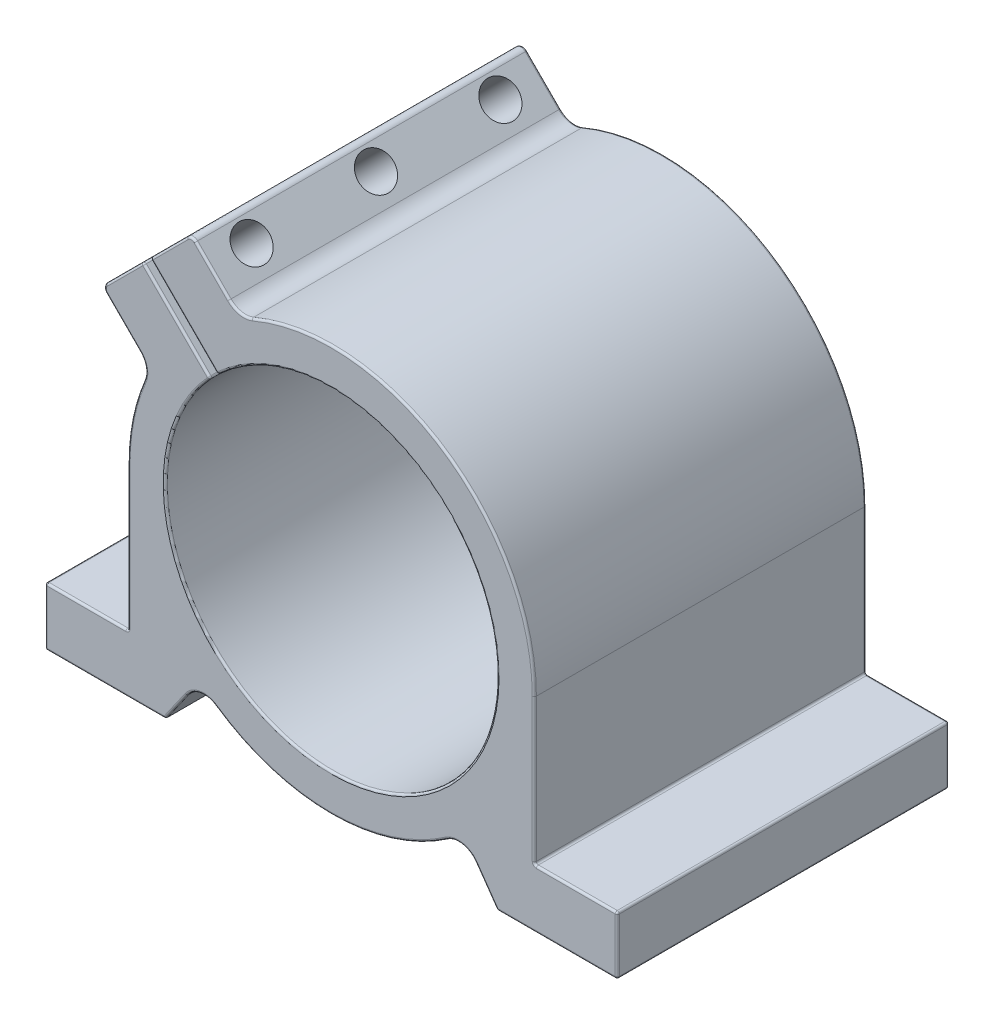
SolidWorks part; units mm, degrees
ref_plane "Спереди" through (0, 0, 0) normal (0, 0, 1) x (1, 0, 0)
ref_plane "Сверху" through (0, 0, 0) normal (0, 1, 0) x (1, 0, 0)
ref_plane "Справа" through (0, 0, 0) normal (1, 0, 0) x (0, 0, -1)
sketch "Эскиз1" plane through (0, 0, 0) normal (0, 0, 1) x (1, 0, 0)
  line L0 (165.1506, 443.0816) -> (1085.1506, 443.0816) construction
  line L1 (0, 0) -> (0, -49) construction
  line L2 (69, -49) -> (-69, -49)
  line L3 (-69, -49) -> (-69, -35)
  line L4 (-69, -35) -> (-49, -35)
  line L5 (-49, -35) -> (-49, 0)
  line L6 (-45.4178, 43.65) -> (-0.8839, -0.8839)
  line L7 (-45.4178, 43.65) -> (-55.3173, 33.7505)
  line L8 (-0.8839, -0.8839) -> (-10.7834, -10.7834)
  line L9 (-55.3173, 33.7505) -> (-10.7834, -10.7834)
  line L10 (-43.65, 45.4178) -> (0.8839, 0.8839)
  line L11 (-43.65, 45.4178) -> (-33.7505, 55.3173)
  line L12 (0.8839, 0.8839) -> (10.7834, 10.7834)
  line L13 (-33.7505, 55.3173) -> (10.7834, 10.7834)
  line L14 (-40, -49) -> (-31.7957, -37.2831)
  line L15 (49, -35) -> (49, 0)
  line L16 (69, -35) -> (49, -35)
  line L17 (69, -49) -> (69, -35)
  line L18 (40, -49) -> (31.7957, -37.2831)
  circle A0 centre (0, 0) radius 40
  circle A1 centre (0, 0) radius 49
  point P11 (-27.3866, 29.1543)
  dimension "D1" = 80
  dimension "D2" = 49
  dimension "D3" = 23
  dimension "D4" = 2.5
  dimension "D5" = 1.25
  dimension "D6" = 1.25
  dimension "D7" = 14
  dimension "D8" = 14
  dimension "D9" = 20
  dimension "D10" = 138
  dimension "D11" = 45
  dimension "D12" = 14
  dimension "D13" = 55
  dimension "D14" = 29
extrude "Бобышка-Вытянуть1" add sketch "Эскиз1" along normal mid plane 80 contours A1 L5 L4 L3 L2 L14 | A1 L13 A0 L9 | A1 L18 L2 L17 L16 L15 | A1 L6 L7 L9 | A1 L13 L11 L10 | L6 A1 L9 A0 | L13 A1 L10 A0
fillet "Скругление1" radius 5 4 edges at (31.7957, -37.2831, 0) (-31.7957, -37.2831, 0) (-43.7109, 22.1441, 0) (-22.1441, 43.7109, 0)
sketch "Эскиз2" plane through (10.7834, 10.7834, 0) normal (0.7071, 0.7071, 0) x (0, 0, -1)
  line L0 (-40, 56.5199) -> (40, 56.5199) construction
  line L1 (-40, 62.9805) -> (-40, 50.0593) construction
  line L2 (40, 62.9805) -> (40, 50.0593) construction
  circle A0 centre (-30, 56.5199) radius 4.25
  circle A1 centre (0, 56.5199) radius 4.25
  circle A2 centre (30, 56.5199) radius 4.25
  dimension "D1" = 8.5
  dimension "D2" = 30
  dimension "D3" = 30
extrude "Вырез-Вытянуть1" cut sketch "Эскиз2" against normal up to surface (16.5 mm away) up to face at (-37.2861, 35.5183, 0)
sketch "Эскиз3" plane through (-0.8839, -0.8839, 0) normal (0.7071, 0.7071, 0) x (0, 0, -1)
  circle A0 centre (-30, 56.5199) radius 3.1
  circle A1 centre (0, 56.5199) radius 3.1
  circle A2 centre (30, 56.5199) radius 3.1
  dimension "D1" = 6.2
extrude "Вырез-Вытянуть2" cut sketch "Эскиз3" against normal blind 80
fillet "Скругление2" radius 1.5 2 edges at (-55.3173, 33.7505, 0) (-33.7505, 55.3173, 0)
fillet "Скругление3" radius 0.5 64 edges at (40, -49, 0) (-40, -49, 0) (69, -49, 0) (69, -35, 0) (-69, -35, 0) (-69, -49, 0) (-44.8083, 22.0335, -40) (-48.0184, 9.7588, -40) (-49, -17.5, -40) (-59, -35, -40) (-69, -42, -40) (-54.5, -49, -40) (-37.3952, -45.28, -40) (-31.5784, -39.5066, -40) (0, -49, -40) (31.5784, -39.5066, -40) (37.3952, -45.28, -40) (54.5, -49, -40) (69, -42, -40) (59, -35, -40) (49, -17.5, -40) (27.0536, 40.8547, -40) (-22.0335, 44.8083, -40) (-28.6519, 50.2187, -40) (-33.7505, 54.696, -40) (-39.2306, 49.8372, -40) (-35.5183, 37.2861, -40) (-37.2861, 35.5183, -40) (-49.8372, 39.2306, -40) (-54.696, 33.7505, -40) (-50.2187, 28.6519, -40) (-27.3866, 29.1543, 0) (-29.1543, 27.3866, 0) (28.2843, -28.2843, -40) (-37.2861, 35.5183, 40) (28.2843, -28.2843, 40) (-35.5183, 37.2861, 40) (-39.2306, 49.8372, 40) (-33.7505, 54.696, 40) (-28.6519, 50.2187, 40) (-22.0335, 44.8083, 40) (27.0536, 40.8547, 40) (49, -17.5, 40) (59, -35, 40) (69, -42, 40) (54.5, -49, 40) (37.3952, -45.28, 40) (31.5784, -39.5066, 40) (0, -49, 40) (-31.5784, -39.5066, 40) (-37.3952, -45.28, 40) (-54.5, -49, 40) (-69, -42, 40) (-59, -35, 40) (-49, -17.5, 40) (-48.0184, 9.7588, 40) (-44.8083, 22.0335, 40) (-50.2187, 28.6519, 40) (-54.696, 33.7505, 40) (-49.8372, 39.2306, 40) (49, -35, 0) (-49, -35, 0) (-43.65, 45.4178, 0) (-45.4178, 43.65, 0)
